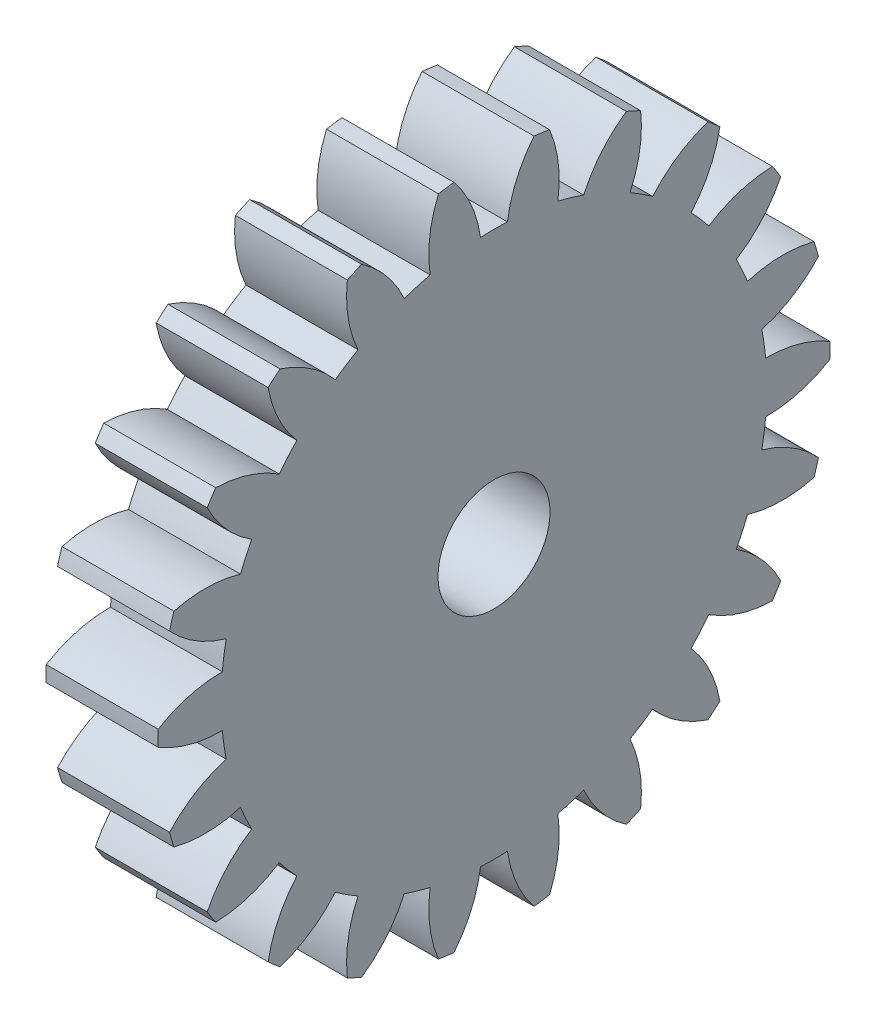
SolidWorks part; units mm, degrees
ref_plane "Plane1" through (0, 0, 0) normal (0, 0, 1) x (1, 0, 0)
ref_plane "Plane2" through (0, 0, 0) normal (0, 1, 0) x (1, 0, 0)
ref_plane "Plane3" through (0, 0, 0) normal (1, 0, 0) x (0, 0, -1)
sketch "HoldingSke" plane through (0, 0, 0) normal (0, 1, 0) x (1, 0, 0)
  line L0 (0, 0) -> (3.7087, -1.4984)
  line L1 (-15, 0) -> (100, 0) construction
  line L2 (0, 0) -> (-2.1039, 2.3779)
  line L3 (0, 0) -> (-11.863, 4.5341)
  line L4 (0, 0) -> (8.0072, 3.2351)
  line L5 (0, 0) -> (-46.8476, -17.4728)
  line L6 (0, 0) -> (-0.829, -0.5593)
  line L7 (-2.1039, 2.3779) -> (8.6586, 51.2059)
  line L8 (-76.2, 54.61) -> (-76.1, 54.61)
  line L9 (-71.009, 38.7566) -> (-53.1078, 45.2721)
  line L10 (-76.2, 71.12) -> (104.1128, 71.12)
  line L11 (0, 0) -> (-1, 0)
  line L12 (-76.2, 101.6) -> (-76.192, 101.6)
  line L13 (24.9733, 27.94) -> (52.9518, 28.4284)
  line L14 (24.9733, 27.94) -> (24.9743, 27.94)
  line L15 (24.9733, 27.94) -> (100.4006, 29.5858)
  line L16 (-63.627, -0.25) -> (-12.827, -0.25)
  circle A0 centre (0, 0) radius 0.5
  circle A1 centre (0, 0) radius 2.4365
  circle A2 centre (0, 0) radius 37.5
  circle A3 centre (0, 0) radius 0.5
  dimension "MHD" = 4.873
  dimension "Hub_dia" = 75
  dimension "Bore" = 1
  dimension "MBD" = 1
  dimension "Num_teeth" = 22
  dimension "Pitch" = 4
  dimension "Overall_len" = 50
  dimension "Show_teeth" = 22
  dimension "Thickness" = 1
  dimension "OAL" = 50.0001
  dimension "T_dim" = 0.1
  dimension "Ap" = 20
  dimension "H" = 19.05
  dimension "Pitch_radius" = 180.3128
  dimension "Width" = 1
  dimension "Backlash" = 0.008
  dimension "Addendum_fac" = 1
  dimension "Dedendum_fac" = 1.25
  dimension "Clearance_fac" = 0.25
  dimension "Dedendum_add" = 0.001
  dimension "Module" = 0.25
sketch "BasProSke" plane through (0, 0, 0) normal (0, 1, 0) x (1, 0, 0)
  line L0 (-10, 0) -> (60, 0) construction
  line L1 (0, 0) -> (0, 3)
  line L2 (0, 0) -> (1, 0)
  line L3 (1, 0) -> (1, 3)
  line L4 (1, 3) -> (0, 3)
  dimension "Thickness" = 1
  dimension "Diameter" = 6
revolve "Base-Revolve" add sketch "BasProSke" angle 360 about L0
sketch "TooCutSke" plane through (0, 0, 0) normal (1, 0, 0) x (0, 0, -1)
  line L1 (0, 0) -> (0, 107) construction
  line L2 (0, 0) -> (-0.2102, 2.742) construction
  line L3 (0, 0) -> (-0.781, 5.4321) construction
  line L4 (-0.2102, 2.742) -> (-0.3905, 2.716) construction
  arc A0 (0.1203, 2.4335) -> (-0.1203, 2.4335) centre (0, 0) ccw
  arc A1 (0.3771, 3.0018) -> (-0.3771, 3.0018) centre (0, 0) ccw
  circle A2 centre (0, 0) radius 2.75 construction
  circle A3 centre (0, 0) radius 2.5842 construction
  arc A4 (-0.1203, 2.4335) -> (-0.3771, 3.0018) centre (-1.21, 2.2834) ccw
  arc A5 (0.3771, 3.0018) -> (0.1203, 2.4335) centre (1.21, 2.2834) ccw
  dimension "Root_dia" = 4.873
  dimension "Overcut_dia" = 6.0508
  dimension "Pitch_dia" = 5.5
  dimension "Base_dia" = 5.1683
  dimension "Flank_rad" = 1.1
  dimension "Half_ang" = 8.182
  dimension "Half_CT" = 0.1822
extrude "ToothCut" cut sketch "TooCutSke" along normal through all
fillet "Breaks" [suppressed] radius 0.005
fillet "RootFillets" [suppressed] radius 0.0635
pattern_circular "TeethCuts" count 22 every 16.364 about axis through (-10, 0, 0) along (1, 0, 0) of "ToothCut", "RootFillets", "Breaks"
sketch "HubNeaOneSke" plane through (0, 0, 0) normal (-1, 0, 0) x (0, 0, 1)
  circle A0 centre (0, 0) radius 2.4365
  dimension "Diameter" = 4.873
extrude "HubNearOne" [suppressed] add sketch "HubNeaOneSke" along normal blind 49.0001
sketch "HubNeaBotSke" plane through (0, 0, 0) normal (-1, 0, 0) x (0, 0, 1)
  circle A0 centre (0, 0) radius 2.4365
  dimension "Diameter" = 4.873
extrude "HubNearBoth" [suppressed] add sketch "HubNeaBotSke" along normal blind 24.5
ref_plane "FarPln" through (1, 0, 0) normal (1, 0, 0) x (0, 0, -1)
sketch "HubFarSke" plane through (1, 0, 0) normal (1, 0, 0) x (0, 0, -1)
  circle A0 centre (0, 0) radius 2.4365
  dimension "Diameter" = 4.873
extrude "HubFar" [suppressed] add sketch "HubFarSke" along normal blind 24.5
sketch "BorSke" plane through (0, 0, 0) normal (1, 0, 0) x (0, 0, -1)
  circle A0 centre (0, 0) radius 0.5
  dimension "Diameter" = 1
extrude "Bore" cut sketch "BorSke" along normal mid plane 100.0001
sketch "KeySke" plane through (0, 0, 0) normal (1, 0, 0) x (0, 0, -1)
  line L0 (-0.05, 0) -> (-0.05, 0.6)
  line L1 (-0.05, 0.6) -> (0.05, 0.6)
  line L2 (0.05, 0.6) -> (0.05, 0)
  line L3 (0, 0) -> (0, 34) construction
  line L4 (-0.05, 0) -> (0.05, 0)
  dimension "Offset" = 0.6
extrude "Keyway" [suppressed] cut sketch "KeySke" along normal mid plane 100.0001
pattern_circular "Keyway2" [suppressed] count 2 every 90 about axis through (-10, 0, 0) along (1, 0, 0)
equation "' \"Module@HoldingSke\" = 6.35"
equation "' \"Num_teeth@HoldingSke\" = 12"
equation "' \"Ap@HoldingSke\" =  20"
equation "' \"Ap@HoldingSke\" = 20"
equation "' \"Width@HoldingSke\" = 0.5 * 25.4"
equation "' \"Hub_dia@HoldingSke\"= 1 * 25.4"
equation "' \"Hub_dia@HoldingSke\" = 1 * 25.4"
equation "' \"Overall_len@HoldingSke\" = 1.0 * 25.4"
equation "' \"Bore@HoldingSke\" = 0.75 * 25.4"
equation "' \"T_dim@HoldingSke\" = 0.1 * 25.4"
equation "' \"Width@KeySke\" = 0.25 * 25.4"
equation "' \"Show_teeth@HoldingSke\" = 13"
equation "' \"Backlash@HoldingSke\" = 0.009 * 25.4"
equation "' \"Addendum_fac@HoldingSke\" = 1.0"
equation "' \"Dedendum_fac@HoldingSke\" = 1.25"
equation "' \"Dedendum_add@HoldingSke\" = 0.00005 * 25.4"
equation "' \"Clearance_fac@HoldingSke\" = 0.25"
equation "\"Pitch@HoldingSke\" = 1 / \"Module@HoldingSke\""
equation "\"Overcut_dia@TooCutSke\" = (\"Num_teeth@HoldingSke\" + 2 * \"Addendum_fac@HoldingSke\") / \"Pitch@HoldingSke\" + 0.002 * 25.4"
equation "\"Pitch_dia@TooCutSke\" = \"Num_teeth@HoldingSke\" / \"Pitch@HoldingSke\""
equation "\"Base_dia@TooCutSke\" = \"Num_teeth@HoldingSke\" / \"Pitch@HoldingSke\" * cos((\"Ap@HoldingSke\"  * 3.14159265 / 180))"
equation "\"Root_dia@TooCutSke\" = (\"Num_teeth@HoldingSke\" + 2) / \"Pitch@HoldingSke\" - 2 * (\"Addendum_fac@HoldingSke\" + \"Dedendum_fac@HoldingSke\") / \"Pitch@HoldingSke\" - \"Dedendum_add@HoldingSke\" * 2"
equation "\"Half_ang@TooCutSke\" = 180 / \"Num_teeth@HoldingSke\""
equation "\"Half_CT@TooCutSke\" = \"Num_teeth@HoldingSke\" / \"Pitch@HoldingSke\" * sin((3.14159265 / 2 / \"Num_teeth@HoldingSke\")) / 2 - 7 * \"Backlash@HoldingSke\" / 4"
equation "\"Flank_rad@TooCutSke\" = \"Num_teeth@HoldingSke\" / \"Pitch@HoldingSke\" / 5"
equation "\"Radius@RootFillets\" = \"Clearance_fac@HoldingSke\" / \"Pitch@HoldingSke\" + \"Dedendum_add@HoldingSke\""
equation "\"Break_rad@Breaks\" = 0.02 / \"Pitch@HoldingSke\""
equation "\"Thickness@HoldingSke\" = \"Width@HoldingSke\""
equation "\"OAL@HoldingSke\" = \"Thickness@HoldingSke\""
equation "\"MHD@HoldingSke\" = (\"Num_teeth@HoldingSke\" + 2) / \"Pitch@HoldingSke\" - 2 * (\"Addendum_fac@HoldingSke\" + \"Dedendum_fac@HoldingSke\")  / \"Pitch@HoldingSke\" - \"Dedendum_add@HoldingSke\" * 2"
equation "\"MBD@HoldingSke\" = (\"Num_teeth@HoldingSke\" + 2) / \"Pitch@HoldingSke\" - 2 * (\"Addendum_fac@HoldingSke\" + \"Dedendum_fac@HoldingSke\")  / \"Pitch@HoldingSke\" - \"Dedendum_add@HoldingSke\" * 2 - 0.002 * 25.4"
equation "\"MHD@HoldingSke\" = ((sgn( \"MHD@HoldingSke\" - \"Hub_dia@HoldingSke\" )-1)*( \"MHD@HoldingSke\" - \"Hub_dia@HoldingSke\" ))/-2+ \"Hub_dia@HoldingSke\""
equation "\"MBD@HoldingSke\" = ((sgn( \"MBD@HoldingSke\" - \"Bore@HoldingSke\" )-1)*( \"MBD@HoldingSke\" - \"Bore@HoldingSke\" ))/-2+ \"Bore@HoldingSke\""
equation "\"OAL@HoldingSke\" = ((sgn( \"OAL@HoldingSke\" - \"Overall_len@HoldingSke\" )+1)*( \"OAL@HoldingSke\" - \"Overall_len@HoldingSke\" ))/2 + \"Overall_len@HoldingSke\" + 0.000002 * 25.4"
equation "\"Num_teeth@TeethCuts\" = int( \"Show_teeth@HoldingSke\" ) + 1"
equation "\"Num_teeth@TeethCuts\" = ((sgn( \"Num_teeth@TeethCuts\" - \"Num_teeth@HoldingSke\" )-1)*( \"Num_teeth@TeethCuts\" - \"Num_teeth@HoldingSke\" ))/-2+ \"Num_teeth@HoldingSke\""
equation "\"Num_teeth@TeethCuts\" = ((sgn( \"Num_teeth@TeethCuts\" - 2.0)+1)*( \"Num_teeth@TeethCuts\" - 2.0))/2 +2.0"
equation "\"Angle@TeethCuts\" = 360.0 / \"Num_teeth@HoldingSke\""
equation "\"Diameter@BasProSke\" = (\"Num_teeth@HoldingSke\" + 2 * \"Addendum_fac@HoldingSke\") / \"Pitch@HoldingSke\""
equation "\"Thickness@BasProSke\"  = \"Thickness@HoldingSke\""
equation "' \"Fillet_rad@BasProSke\" =  \"Thickness@HoldingSke\" * 0.05"
equation "' \"Fillet_rad@BasProSke\" = \"Thickness@HoldingSke\" * 0.05"
equation "\"MHD@HoldingSke\" = ((sgn( \"MHD@HoldingSke\" - \"Root_dia@TooCutSke\" )-1)*( \"MHD@HoldingSke\" - \"Root_dia@TooCutSke\" ))/-2+ \"Root_dia@TooCutSke\""
equation "\"Diameter@HubNeaOneSke\" = \"MHD@HoldingSke\""
equation "\"Length@HubNearOne\" = \"OAL@HoldingSke\" - \"Thickness@BasProSke\""
equation "\"Diameter@HubNeaBotSke\" = \"MHD@HoldingSke\""
equation "\"Length@HubNearBoth\" = ( \"OAL@HoldingSke\" - \"Thickness@BasProSke\" ) / 2.0"
equation "\"Thickness@FarPln\" = \"Thickness@BasProSke\""
equation "\"Diameter@HubFarSke\" = \"MHD@HoldingSke\""
equation "\"Length@HubFar\" = ( \"OAL@HoldingSke\" - \"Thickness@BasProSke\" ) / 2.0"
equation "\"Diameter@BorSke\" = \"MBD@HoldingSke\""
equation "\"D1@Bore\" = \"OAL@HoldingSke\" * 2.0"
equation "\"D1@Keyway\" = \"OAL@HoldingSke\" * 2.0"
equation "\"Offset@KeySke\" = \"T_dim@HoldingSke\" + \"MBD@HoldingSke\" / 2.0"
